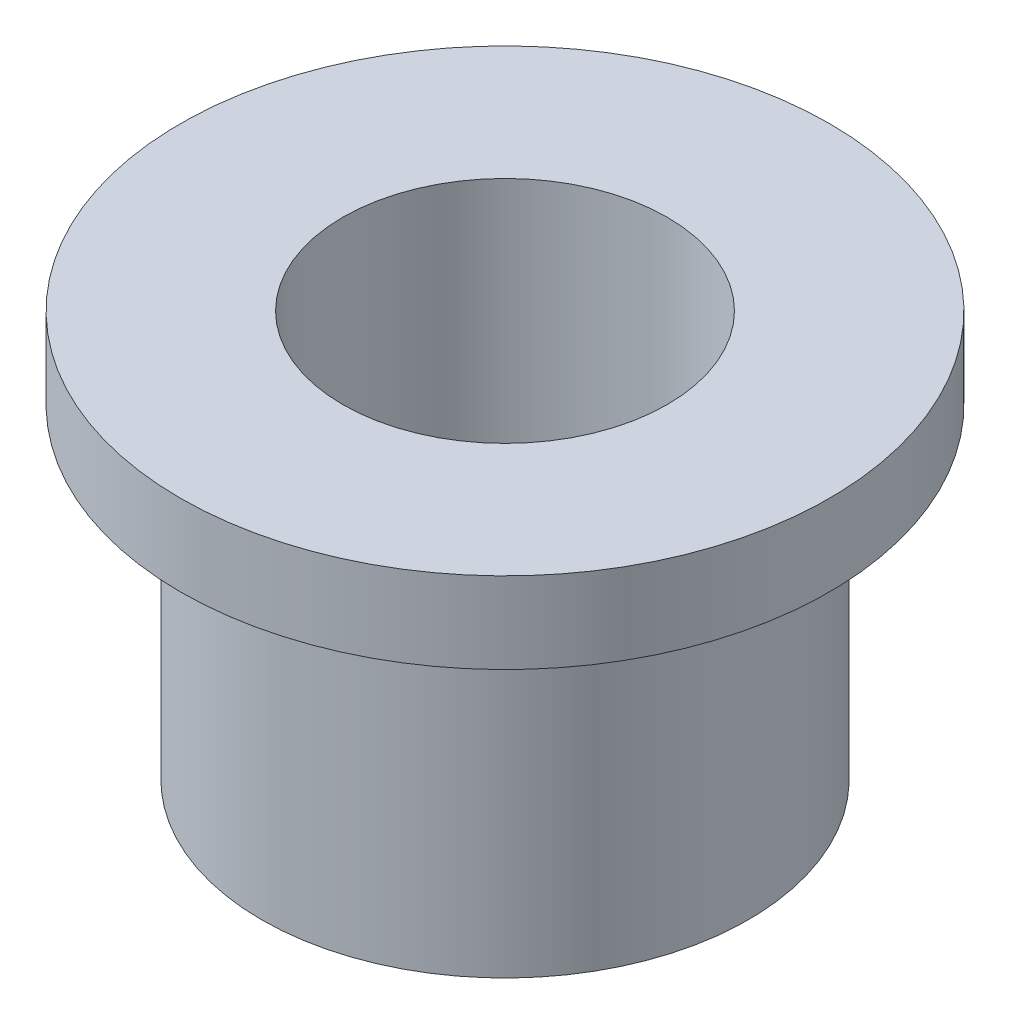
SolidWorks part; units mm, degrees
ref_plane "Front Plane" through (0, 0, 0) normal (0, 0, 1) x (1, 0, 0)
ref_plane "Top Plane" through (0, 0, 0) normal (0, 1, 0) x (1, 0, 0)
ref_plane "Right Plane" through (0, 0, 0) normal (1, 0, 0) x (0, 0, -1)
sketch "Sketch1" plane through (0, 0, 0) normal (0, 0, 1) x (1, 0, 0)
  line L0 (0, 167.3838) -> (0, -78.2596) construction
  line L2 (-50, 0) -> (-50, 125)
  line L4 (-50, 0) -> (-75, 0)
  line L5 (-75, 0) -> (-75, 100)
  line L6 (-75, 100) -> (-100, 100)
  line L7 (-100, 100) -> (-100, 125)
  line L8 (-100, 125) -> (-50, 125)
  dimension "D1" = 100
  dimension "D2" = 25
  dimension "D3" = 125
  dimension "D4" = 50
  dimension "D5" = 75
revolve "Revolve1" add sketch "Sketch1" angle 360 about L0
